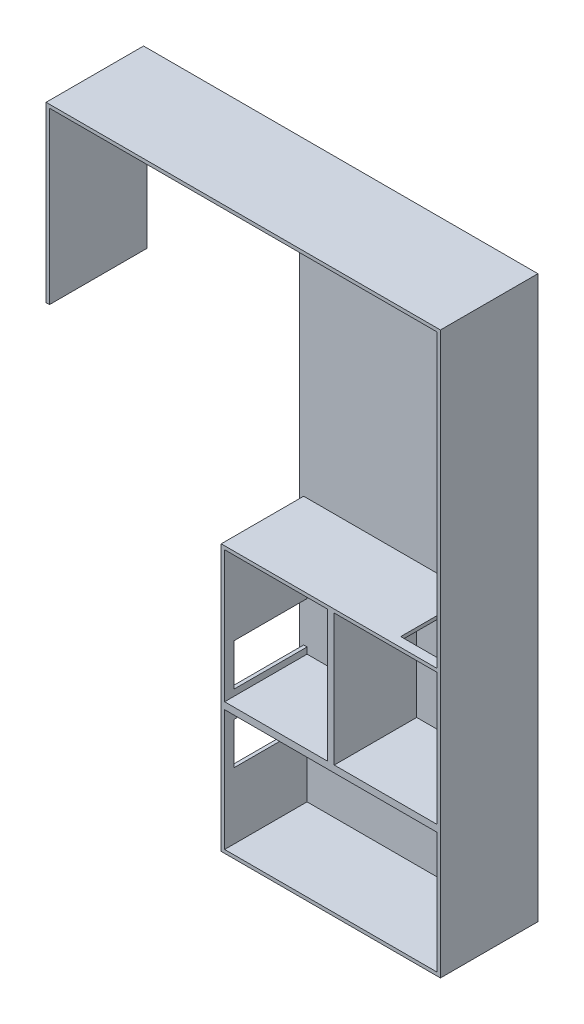
SolidWorks part; units mm, degrees
ref_plane "Front Plane" through (0, 0, 0) normal (0, 0, 1) x (1, 0, 0)
ref_plane "Top Plane" through (0, 0, 0) normal (0, 1, 0) x (1, 0, 0)
ref_plane "Right Plane" through (0, 0, 0) normal (1, 0, 0) x (0, 0, -1)
ref_plane "Plane1" through (0, 0, 38431.7002) normal (0, 0, -1) x (-1, 0, 0)
sketch "Sketch1" plane through (0, 0, 38431.7002) normal (0, 0, -1) x (-1, 0, 0)
  line L0 (14521.6177, 19917.4814) -> (14521.6177, -20082.5186)
  line L1 (7996.6177, 19917.4814) -> (42361.227, 19917.4814)
  line L2 (7996.6177, 19917.4814) -> (7996.6177, -23832.5186)
  line L3 (7996.6177, -23832.5186) -> (42361.227, -23832.5186)
  line L4 (42361.227, 19917.4814) -> (42361.227, -23832.5186)
  line L5 (14521.6177, -20082.5186) -> (42361.227, -20082.5186)
  line L6 (42361.227, -20082.5186) -> (37444.5603, 19917.4814)
  line L7 (37444.5603, 19917.4814) -> (14521.6177, 19917.4814)
  line L8 (14521.6177, 3507.4814) -> (7996.6177, 3507.4814)
  line L9 (14521.6177, 19917.4814) -> (14521.6177, 3507.4814)
  dimension "D1" = 11550
  dimension "D2" = 3750
  dimension "D3" = 27340
extrude "Boss-Extrude1" add sketch "Sketch1" against normal up to surface (440 mm away) contours L8 L0 L1 L2
sketch "Sketch2" plane through (0, 0, 38431.7002) normal (0, 0, -1) x (-1, 0, 0)
  line L0 (7996.6177, 3507.4814) -> (7996.6177, 19917.4814) construction
  line L1 (7996.6177, 7247.4814) -> (14406.6177, 7247.4814)
  line L2 (7996.6177, 7247.4814) -> (7996.6177, 11297.4814)
  line L3 (7996.6177, 11297.4814) -> (14406.6177, 11297.4814)
  line L4 (14406.6177, 7247.4814) -> (14406.6177, 11297.4814)
  line L5 (11201.6177, 9272.4814) -> (14406.6177, 9272.4814) construction
  line L6 (7996.6177, 7247.4814) -> (11201.6177, 7247.4814)
  line L7 (7996.6177, 7247.4814) -> (7996.6177, 11297.4814)
  line L9 (11201.6177, 7247.4814) -> (11201.6177, 11297.4814)
  line L10 (11201.6177, 9272.4814) -> (7996.6177, 9272.4814) construction
  line L11 (11101.6177, 7347.4814) -> (11201.6177, 7347.4814) construction
  line L12 (8096.6177, 7347.4814) -> (11101.6177, 7347.4814)
  line L13 (8096.6177, 7347.4814) -> (8096.6177, 11197.4814)
  line L14 (8096.6177, 11197.4814) -> (11101.6177, 11197.4814)
  line L15 (11101.6177, 7347.4814) -> (11101.6177, 11197.4814)
  line L16 (8096.6177, 7347.4814) -> (11101.6177, 11197.4814) construction
  line L17 (8096.6177, 11197.4814) -> (11101.6177, 7347.4814) construction
  line L18 (11101.6177, 7347.4814) -> (11101.6177, 7247.4814) construction
  line L19 (14306.6177, 7347.4814) -> (11301.6177, 7347.4814)
  line L20 (14306.6177, 7347.4814) -> (14306.6177, 11197.4814)
  line L21 (14306.6177, 11197.4814) -> (11301.6177, 11197.4814)
  line L22 (11301.6177, 7347.4814) -> (11301.6177, 11197.4814)
  line L23 (14306.6177, 3607.4814) -> (14406.6177, 3607.4814) construction
  line L24 (7996.6177, 7247.4814) -> (14406.6177, 7247.4814)
  line L25 (7996.6177, 7247.4814) -> (7996.6177, 3507.4814)
  line L26 (7996.6177, 3507.4814) -> (14406.6177, 3507.4814)
  line L27 (14406.6177, 7247.4814) -> (14406.6177, 3507.4814)
  line L28 (8096.6177, 3607.4814) -> (14306.6177, 3607.4814)
  line L29 (8096.6177, 3607.4814) -> (8096.6177, 7147.4814)
  line L30 (8096.6177, 7147.4814) -> (14306.6177, 7147.4814)
  line L31 (14306.6177, 3607.4814) -> (14306.6177, 7147.4814)
  line L32 (14306.6177, 3607.4814) -> (14306.6177, 3507.4814) construction
  line L33 (14306.6177, 7147.4814) -> (14306.6177, 7247.4814) construction
  line L34 (7996.6177, 19917.4814) -> (19527.2909, 19917.4814)
  line L39 (7996.6177, 19917.4814) -> (7996.6177, 3507.4814) construction
  line L40 (19527.2909, 19917.4814) -> (19527.2909, 14843.3368)
  line L41 (7996.6177, 11297.4814) -> (7996.6177, 19917.4814)
  line L42 (7996.6177, 11297.4814) -> (8096.6177, 11297.4814)
  line L43 (19527.2909, 14843.3368) -> (19427.2909, 14843.3368)
  line L44 (19427.2909, 14843.3368) -> (19427.2909, 19817.4814)
  line L49 (19427.2909, 19817.4814) -> (8096.6177, 19817.4814)
  line L50 (8096.6177, 19817.4814) -> (8096.6177, 11297.4814)
  line L51 (14521.6177, 19917.4814) -> (7996.6177, 19917.4814) construction
  line L52 (8096.6177, 19817.4814) -> (8096.6177, 19917.4814) construction
  line L53 (8096.6177, 19817.4814) -> (7996.6177, 19817.4814) construction
  line L54 (19427.2909, 19817.4814) -> (19527.2909, 19817.4814) construction
  point P11 (9599.1177, 9272.4814)
  point P41 (8111.6783, 19801.7252)
  point P47 (8096.6177, 11297.4814)
  point P48 (19527.2909, 19917.4814)
  dimension "D1" = 3370
  dimension "D3" = 4050
  dimension "D4" = 100
  dimension "D5" = 3740
ref_plane "Plane2" through (0, 0, 40421.7002) normal (0, 0, 1) x (1, 0, 0)
sketch "Sketch3" plane through (0, 0, 40421.7002) normal (0, 0, 1) x (1, 0, 0)
  line L0 (-7996.6177, 3507.4814) -> (-7996.6177, 19917.4814) construction
  line L1 (-7996.6177, 3207.4814) -> (-15706.6177, 3207.4814)
  line L2 (-7996.6177, 3207.4814) -> (-7996.6177, -1892.5186)
  line L3 (-7996.6177, -1892.5186) -> (-15706.6177, -1892.5186)
  line L4 (-15706.6177, 3207.4814) -> (-15706.6177, -1892.5186)
  line L5 (-7996.6177, 3507.4814) -> (-14406.6177, 3507.4814) construction
  line L7 (-14406.6177, 7247.4814) -> (-14406.6177, 3507.4814) construction
  dimension "D1" = 300
  dimension "D2" = 1300
  dimension "D3" = 5100
extrude "Boss-Extrude2" add sketch "Sketch2" against normal blind 2850 contours L9 L1 L4 L3 L19 L22 L21 L20 | L27 L1 L25 L26 L31 L28 L29 L30 | L1 L9 L3 L2 L15 L12 L13 L14 | L41 L34 L40 L43 L44 L49 L50 L42
sketch "Sketch6" plane through (-14406.6177, 0, 0) normal (-1, 0, 0) x (0, 0, 1)
  line L0 (38871.7002, 3507.4814) -> (38871.7002, 11297.4814) construction
  line L1 (41006.7002, 8755.1082) -> (38871.7002, 8755.1082)
  line L2 (41006.7002, 8755.1082) -> (41006.7002, 7531.1082)
  line L3 (41006.7002, 7531.1082) -> (38871.7002, 7531.1082)
  line L4 (38871.7002, 8755.1082) -> (38871.7002, 7531.1082)
  line L6 (41281.7002, 7147.4814) -> (38871.7002, 7147.4814) construction
  line L7 (41006.7002, 6763.8545) -> (38871.7002, 6763.8545)
  line L8 (38871.7002, 5539.8545) -> (38871.7002, 6763.8545)
  line L9 (41006.7002, 5539.8545) -> (41006.7002, 6763.8545)
  line L10 (41006.7002, 5539.8545) -> (38871.7002, 5539.8545)
  point P4 (0, 0)
  point P7 (38871.7002, 7658.6388)
  dimension "D1" = 2135
  dimension "D2" = 1224
extrude "Cut-Extrude2" cut sketch "Sketch6" against normal blind 1036
sketch "Sketch7" plane through (0, 11297.4814, 0) normal (0, 1, 0) x (1, 0, 0)
  line L1 (-9433.1157, -38871.7002) -> (-8208.1157, -38871.7002)
  line L2 (-9433.1157, -38871.7002) -> (-9433.1157, -41006.7002)
  line L3 (-9433.1157, -41006.7002) -> (-8208.1157, -41006.7002)
  line L4 (-8208.1157, -38871.7002) -> (-8208.1157, -41006.7002)
  line L5 (-9433.1157, -38871.7002) -> (-8208.1157, -41006.7002) construction
  line L6 (-9433.1157, -41006.7002) -> (-8208.1157, -38871.7002) construction
  line L7 (-8096.6177, -38871.7002) -> (-14406.6177, -38871.7002) construction
  point P0 (-8820.6157, -39939.2002)
  point P5 (0, 0)
  point P6 (-8576.0453, -38871.7002)
  point P7 (-8208.1157, -41006.7002)
  point P10 (0, 0)
  dimension "D1" = 2135
  dimension "D2" = 1225
extrude "Cut-Extrude3" cut sketch "Sketch7" against normal blind 1036
